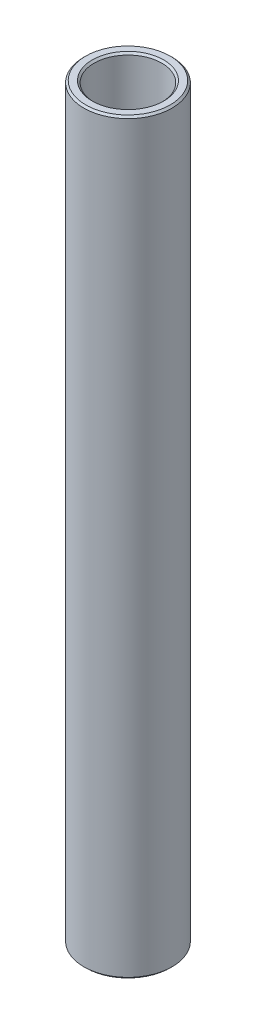
SolidWorks part; units mm, degrees
ref_plane "Front Plane" through (0, 0, 0) normal (0, 0, 1) x (1, 0, 0)
ref_plane "Top Plane" through (0, 0, 0) normal (0, 1, 0) x (1, 0, 0)
ref_plane "Right Plane" through (0, 0, 0) normal (1, 0, 0) x (0, 0, -1)
sketch "Sketch1" plane through (0, 0, 0) normal (0, 0, 1) x (1, 0, 0)
  line L0 (0, 19.068) -> (0, -19.068) construction
  line L1 (2.3, 25.4) -> (2.3, -25.4)
  line L2 (2.3, -25.4) -> (3, -25.4)
  line L3 (3, -25.4) -> (3, 25.4)
  line L4 (3, 25.4) -> (2.3, 25.4)
  point P5 (2.3, 0)
  dimension "D1" = 50.8
  dimension "D2" = 4.6
  dimension "D3" = 6
revolve "Revolve1" add sketch "Sketch1" angle 360 about L0
chamfer "Chamfer1" distance 0.127 angle 45 4 edges at (0, -25.4, 2.3) (0, -25.4, 3) (0, 25.4, 3) (0, 25.4, 2.3)
